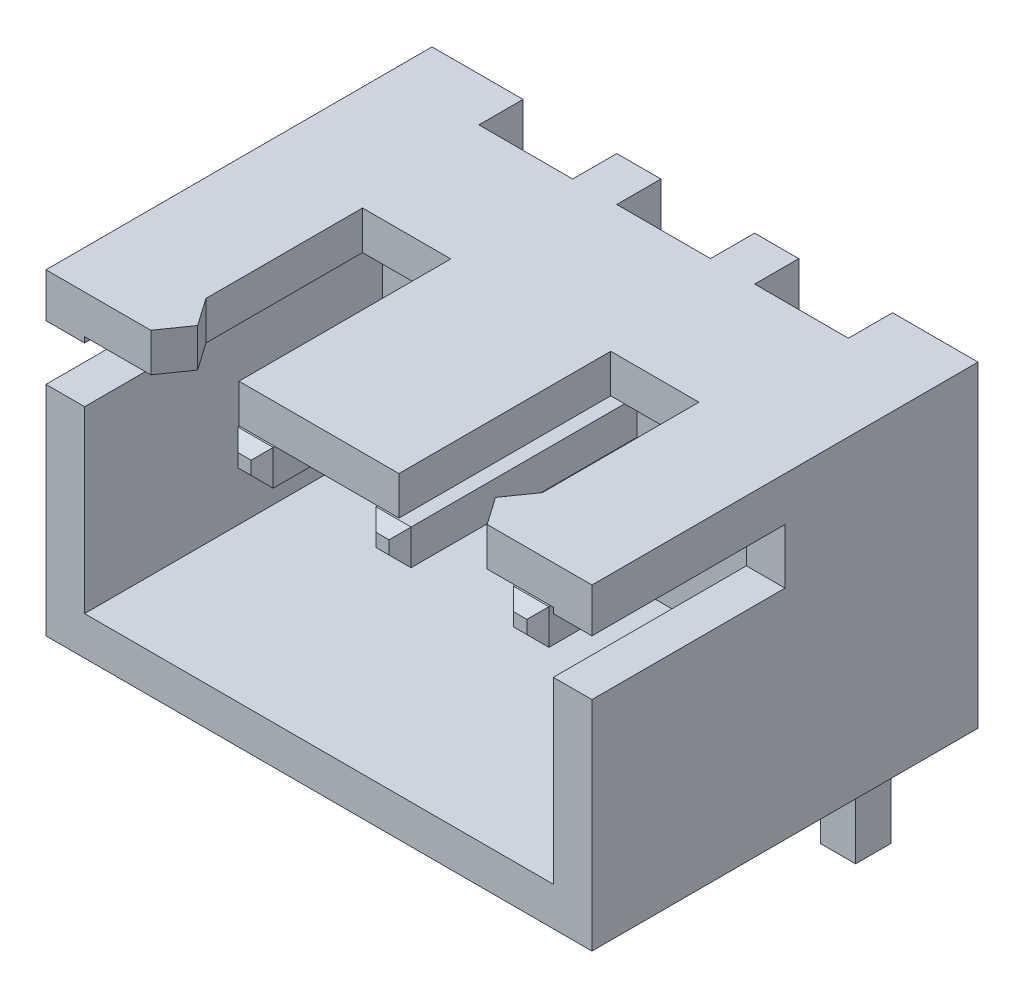
SolidWorks part; units mm, degrees
material "Nylon 6/10"
ref_plane "Front Plane" through (0, 0, 0) normal (0, 0, 1) x (1, 0, 0)
ref_plane "Top Plane" through (0, 0, 0) normal (0, 1, 0) x (1, 0, 0)
ref_plane "Right Plane" through (0, 0, 0) normal (1, 0, 0) x (0, 0, -1)
other "Configuration Table"
sketch "Sketch1" plane through (0, 0, 0) normal (0, 1, 0) x (1, 0, 0)
  line L1 (-4.95, 3.5) -> (4.95, 3.5)
  line L2 (-4.95, 3.5) -> (-4.95, -3.5)
  line L3 (-4.95, -3.5) -> (4.95, -3.5)
  line L4 (4.95, 3.5) -> (4.95, -3.5)
  line L5 (-4.95, 3.5) -> (4.95, -3.5) construction
  line L6 (-4.95, -3.5) -> (4.95, 3.5) construction
  point P0 (0, 0)
  dimension "D1" = 7
  dimension "D2" = 9.9
extrude "Boss-Extrude1" add sketch "Sketch1" along normal mid plane 5.75
shell "Shell1" thickness 0.7
sketch "Sketch2" plane through (0, 0, 0) normal (1, 0, 0) x (0, 0, -1)
  line L0 (-3.5, 2.175) -> (-3.5, -2.175) construction
  line L2 (-3.5, 2.175) -> (-3.5, -2.175) construction
  line L3 (-3.5, 2.875) -> (3.5, 2.875) construction
  line L4 (-3.5, 2.075) -> (0, 2.075)
  line L5 (0, 2.075) -> (0, 1.075)
  line L6 (0, 1.075) -> (-3.5, 1.075)
  line L7 (-3.5, 1.075) -> (-3.5, 2.075)
  line L8 (-3.5, 2.875) -> (3.5, 2.875) construction
  dimension "D1" = 0.8
  dimension "D2" = 1
  dimension "D3" = 3.5
extrude "Cut-Extrude1" cut sketch "Sketch2" against normal through all both and the other way through all
sketch "Sketch3" plane through (0, 0, 0) normal (0, 1, 0) x (1, 0, 0)
  line L0 (-3.05, -3.5) -> (-2.7, -3)
  line L1 (-4.95, -3.5) -> (4.95, -3.5) construction
  line L2 (-2.7, -3) -> (-3.05, -2.5)
  line L3 (-3.05, -2.5) -> (-3.05, 0.34)
  line L4 (-3.05, 0.34) -> (3.05, 0.34)
  line L5 (3.05, 0.34) -> (3.05, -2.5)
  line L6 (3.05, -2.5) -> (2.7, -3)
  line L7 (2.7, -3) -> (3.05, -3.5)
  line L8 (3.05, -3.5) -> (-3.05, -3.5)
  line L9 (4.95, -3.5) -> (4.95, 3.5) construction
  point P9 (0, 0.34)
  point P16 (0, -3.5)
  dimension "D1" = 1.9
  dimension "D2" = 2.25
  dimension "D3" = 3.84
  dimension "D4" = 1
extrude "Cut-Extrude2" cut sketch "Sketch3" along normal through all
sketch "Sketch4" plane through (0, 0, 0) normal (0, 1, 0) x (1, 0, 0)
  line L0 (-4.25, -3.5) -> (4.25, -3.5) construction
  line L1 (-1.45, -3.5) -> (1.45, -3.5)
  line L2 (-1.45, -3.5) -> (-1.45, 0.34)
  line L3 (-1.45, 0.34) -> (1.45, 0.34)
  line L4 (1.45, -3.5) -> (1.45, 0.34)
  line L5 (3.05, 0.34) -> (-3.05, 0.34) construction
  line L6 (3.05, -2.5) -> (3.05, 0.34) construction
  point P8 (0, 0.34)
  dimension "D1" = 1.6
extrude "Boss-Extrude2" add sketch "Sketch4" along normal up to surface (0.7 mm away) from surface at 2.175 up to face at (0, 2.875, 1.4433) starting at face at (0, 2.175, 1.71)
ref_plane "Plane1" through (2.55, 0, 0) normal (1, 0, 0) x (0, 0, -1)
sketch "Sketch5" plane through (2.55, 0, 0) normal (1, 0, 0) x (0, 0, -1)
  line L0 (-3.5, -2.875) -> (3.5, -2.875) construction
  line L1 (3.5, 2.875) -> (2.7, 2.875)
  line L2 (3.5, 2.875) -> (3.5, -2.875)
  line L3 (3.5, -2.875) -> (2.7, -2.875)
  line L4 (2.7, 2.875) -> (2.7, -2.875)
  dimension "D1" = 0.8
extrude "Cut-Extrude3" cut sketch "Sketch5" against normal mid plane 1.7
pattern_linear "LPattern1" count 3 spacing 2.5 along (-1, 0, 0) of "Cut-Extrude3"
sketch "Sketch6" plane through (2.55, 0, 0) normal (1, 0, 0) x (0, 0, -1)
  line L0 (-2.4, 0.845) -> (4, 0.845)
  line L1 (4, 0.845) -> (4, -6.175)
  line L2 (4, -6.175) -> (3.36, -6.175)
  line L3 (3.36, -6.175) -> (3.36, 0.205)
  line L4 (3.36, 0.205) -> (-2.4, 0.205)
  line L5 (-2.4, 0.205) -> (-2.4, 0.845)
  line L6 (-3.5, -2.875) -> (3.5, -2.875) construction
  line L7 (-3.5, 2.875) -> (3.5, 2.875) construction
  line L8 (-3.5, 1.075) -> (-3.5, -2.875) construction
  line L9 (3.5, 2.875) -> (3.5, -2.875) construction
  point P8 (-2.4, 0.525)
  dimension "D1" = 0.64
  dimension "D2" = 3.3
  dimension "D3" = 2.35
  dimension "D4" = 1.1
  dimension "D5" = 0.5
extrude "Boss-Extrude3" add sketch "Sketch6" along normal mid plane 0.64 separate body
fillet "Fillet1" radius 1 1 edges at (2.55, 0.845, -4)
fillet "Fillet2" radius 0.34 1 edges at (2.55, 0.205, -3.36)
chamfer "Chamfer1" distance 0.2 angle 45 8 edges at (2.55, -6.175, -3.36) (2.87, -6.175, -3.68) (2.55, -6.175, -4) (2.23, -6.175, -3.68) (2.55, 0.845, 2.4) (2.87, 0.525, 2.4) (2.55, 0.205, 2.4) (2.23, 0.525, 2.4)
pattern_linear "LPattern2" count 3 spacing 2.5 along (-1, 0, 0) of bodies 107
